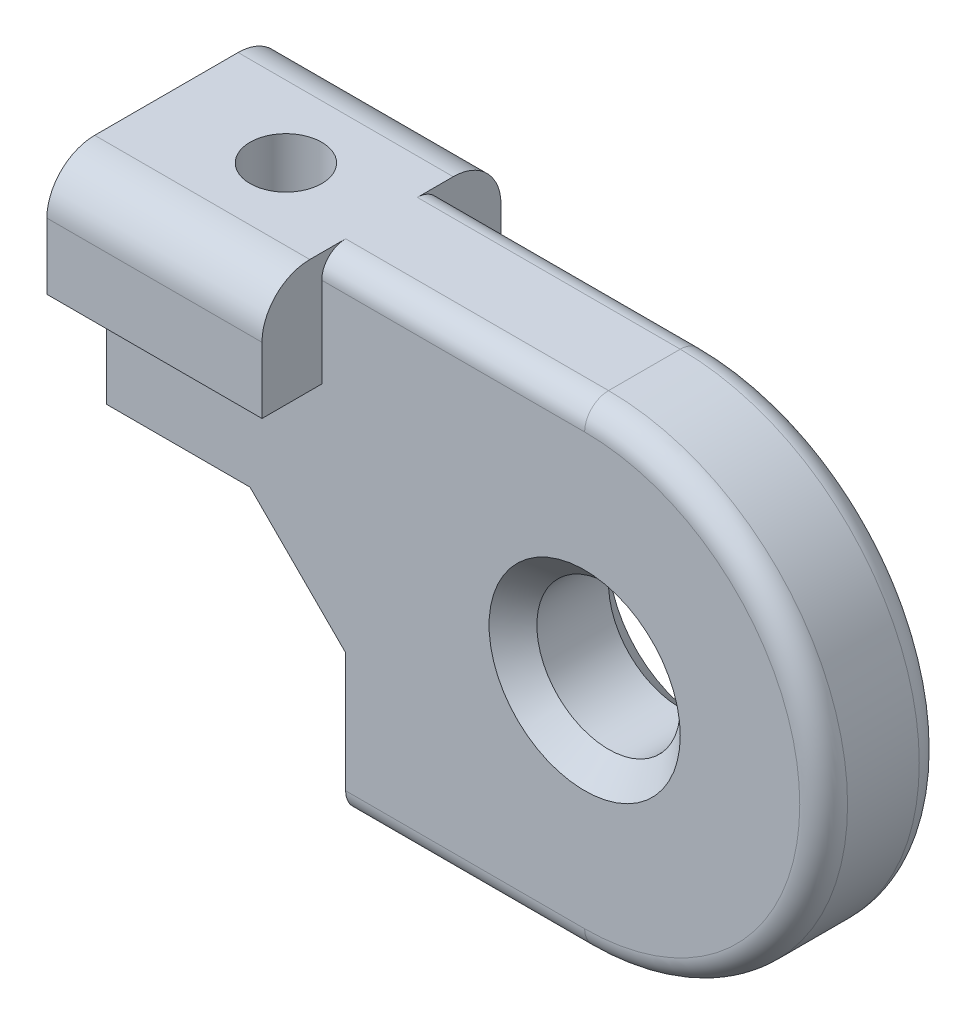
SolidWorks part; units mm, degrees
ref_plane "Front Plane" through (0, 0, 0) normal (0, 0, 1) x (1, 0, 0)
ref_plane "Top Plane" through (0, 0, 0) normal (0, 1, 0) x (1, 0, 0)
ref_plane "Right Plane" through (0, 0, 0) normal (1, 0, 0) x (0, 0, -1)
sketch "Sketch1" plane through (0, 0, 0) normal (0, 0, 1) x (1, 0, 0)
  line L0 (0, 10) -> (-20, 10)
  line L1 (-20, 10) -> (-20, 0)
  line L2 (-10, -10) -> (0, -10)
  line L3 (-20, 0) -> (-14, 0)
  line L4 (55, 0) -> (-55, 0) construction
  line L5 (-10, -4) -> (-10, -10)
  line L6 (-14, 0) -> (-10, -4)
  arc A0 (0, -10) -> (0, 10) centre (0, 0) ccw
  circle A1 centre (0, 0) radius 3
  point P6 (-10, 0)
  dimension "D1" = 20
  dimension "D2" = 6
  dimension "D3" = 20
  dimension "D4" = 10
extrude "Boss-Extrude1" add sketch "Sketch1" along normal mid plane 5
sketch "Sketch2" plane through (0, 0, 0) normal (0, 0, 1) x (1, 0, 0)
  line L0 (-20, 10) -> (-20, 5.2381)
  line L1 (-11, 5.2381) -> (-11, 10)
  line L2 (-11, 10) -> (-20, 10)
  line L5 (-20, 5.2381) -> (-11, 5.2381)
  dimension "D1" = 9
  dimension "D2" = 4.7619
extrude "Boss-Extrude2" add sketch "Sketch2" along normal mid plane 10
fillet "Fillet1" radius 2 2 edges at (-15.5, 10, -5) (-15.5, 10, 5)
chamfer "Chamfer1" distance 1 angle 45 2 edges at (3, 0, -2.5) (3, 0, 2.5)
fillet "Fillet2" radius 1 6 edges at (-5, -10, -2.5) (-5.5, 10, -2.5) (-5, -10, 2.5) (-5.5, 10, 2.5) (10, 0, -2.5) (10, 0, 2.5)
sketch "Sketch3" plane through (0, 10, 0) normal (0, 1, 0) x (1, 0, 0)
  line L0 (-11, 0) -> (11, 0) construction
  line L1 (-20, -3) -> (-20, 3) construction
  circle A0 centre (-15, 0) radius 1.5
  dimension "D1" = 3
  dimension "D2" = 5
extrude "Cut-Extrude1" cut sketch "Sketch3" against normal blind 20
